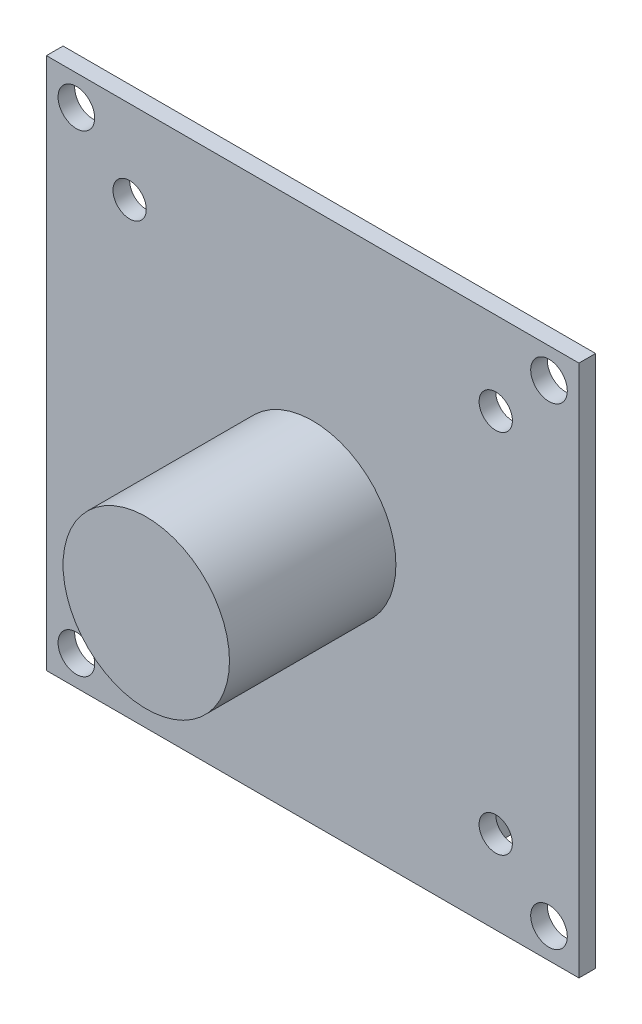
SolidWorks part; units mm, degrees
ref_plane "前视基准面" through (0, 0, 0) normal (0, 0, 1) x (1, 0, 0)
ref_plane "上视基准面" through (0, 0, 0) normal (0, 1, 0) x (1, 0, 0)
ref_plane "右视基准面" through (0, 0, 0) normal (1, 0, 0) x (0, 0, -1)
other "Configuration Table"
sketch "Sketch1" plane through (0, 0, 0) normal (0, 0, 1) x (1, 0, 0)
  line L1 (16, -16) -> (-16, -16)
  line L2 (16, -16) -> (16, 16)
  line L3 (16, 16) -> (-16, 16)
  line L4 (-16, -16) -> (-16, 16)
  line L5 (16, -16) -> (-16, 16) construction
  line L6 (16, 16) -> (-16, -16) construction
  point P0 (0, 0)
  dimension "D1" = 32
  dimension "D2" = 32
extrude "Boss-Extrude1" add sketch "Sketch1" along normal blind 1
sketch "Sketch2" plane through (0, 0, 1) normal (0, 0, 1) x (1, 0, 0)
  line L0 (-16, 11) -> (16, 11) construction
  line L1 (-16, 16) -> (-16, -16) construction
  line L2 (16, -16) -> (16, 16) construction
  line L3 (16, 16) -> (-16, 16) construction
  line L4 (0, 0) -> (-16, 0) construction
  circle A0 centre (-11, 11) radius 1
  circle A1 centre (11, 11) radius 1
  circle A2 centre (11, -11) radius 1
  circle A3 centre (-11, -11) radius 1
  dimension "D2" = 2
  dimension "D3" = 2
  dimension "D1" = 22
  dimension "D4" = 11
  dimension "D5" = 5
extrude "Cut-Extrude1" cut sketch "Sketch2" against normal blind 1 contours A0 | A1 | A2 | A3
sketch "Sketch3" plane through (0, 0, 1) normal (0, 0, 1) x (1, 0, 0)
  circle A0 centre (0, 0) radius 5
  dimension "D1" = 10
extrude "Boss-Extrude2" add sketch "Sketch3" along normal blind 10
sketch "Sketch4" plane through (0, 0, 0) normal (0, 0, -1) x (-1, 0, 0)
  line L0 (16, -16) -> (-16, -16) construction
  line L1 (-8, -10) -> (2, -10)
  line L2 (-8, -10) -> (-8, -14.5)
  line L3 (-8, -14.5) -> (2, -14.5)
  line L4 (2, -10) -> (2, -14.5)
  line L5 (-8, -10) -> (2, -14.5) construction
  line L6 (-8, -14.5) -> (2, -10) construction
  circle A0 centre (-11, -11) radius 1 construction
  point P0 (-3, -12.25)
  point P5 (-3.2165, -9.1078)
  dimension "D1" = 10
  dimension "D2" = 4.5
  dimension "D3" = 3
  dimension "D4" = 1.5
extrude "Boss-Extrude3" add sketch "Sketch4" along normal blind 6
sketch "Sketch5" plane through (0, 0, 1) normal (0, 0, 1) x (1, 0, 0)
  line L0 (16, 16) -> (-16, 16) construction
  line L1 (-16, 16) -> (-16, -16) construction
  line L2 (0, 5) -> (0, -5) construction
  line L3 (-5, 0) -> (5, 0) construction
  circle A0 centre (-14.2, 14.2) radius 1.1
  circle A1 centre (0, 0) radius 5 construction
  circle A2 centre (0, 0) radius 5 construction
  circle A3 centre (14.2, 14.2) radius 1.1
  circle A4 centre (14.2, -14.2) radius 1.1
  circle A5 centre (-14.2, -14.2) radius 1.1
  dimension "D3" = 2.2
  dimension "D1" = 1.8
  dimension "D2" = 1.8
extrude "Cut-Extrude2" cut sketch "Sketch5" against normal blind 2
